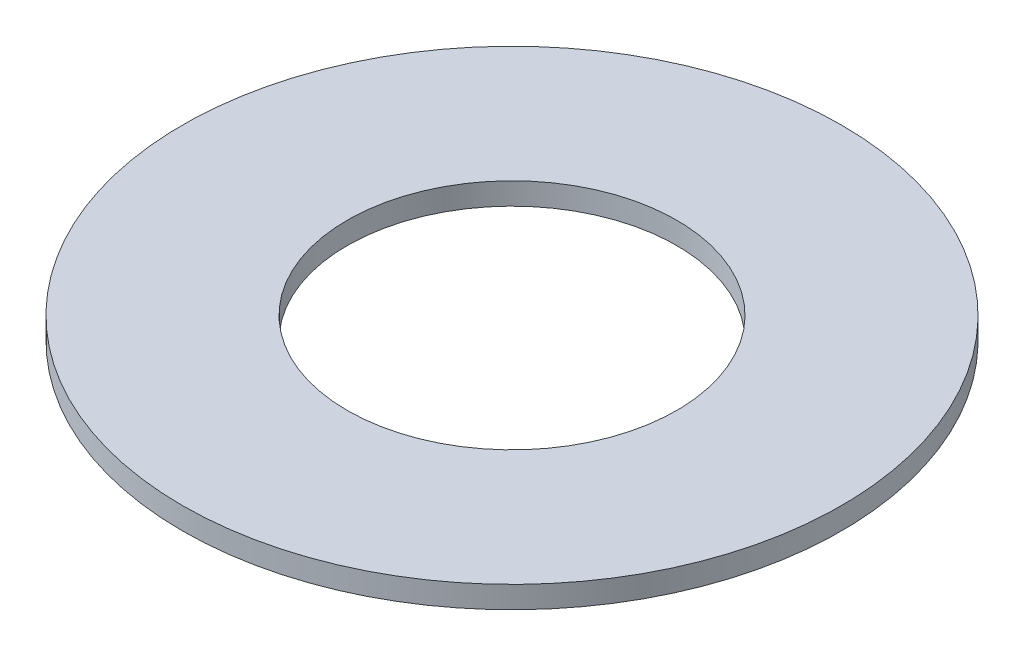
SolidWorks part; units mm, degrees
ref_plane "Front Plane" through (0, 0, 0) normal (0, 0, 1) x (1, 0, 0)
ref_plane "Top Plane" through (0, 0, 0) normal (0, 1, 0) x (1, 0, 0)
ref_plane "Right Plane" through (0, 0, 0) normal (1, 0, 0) x (0, 0, -1)
sketch "Sketch1" plane through (0, 0, 0) normal (0, 1, 0) x (1, 0, 0)
  circle A0 centre (0, 0) radius 6
  circle A1 centre (0, 0) radius 3
  dimension "D1" = 12
  dimension "D2" = 3
extrude "Boss-Extrude1" add sketch "Sketch1" along normal blind 0.4
